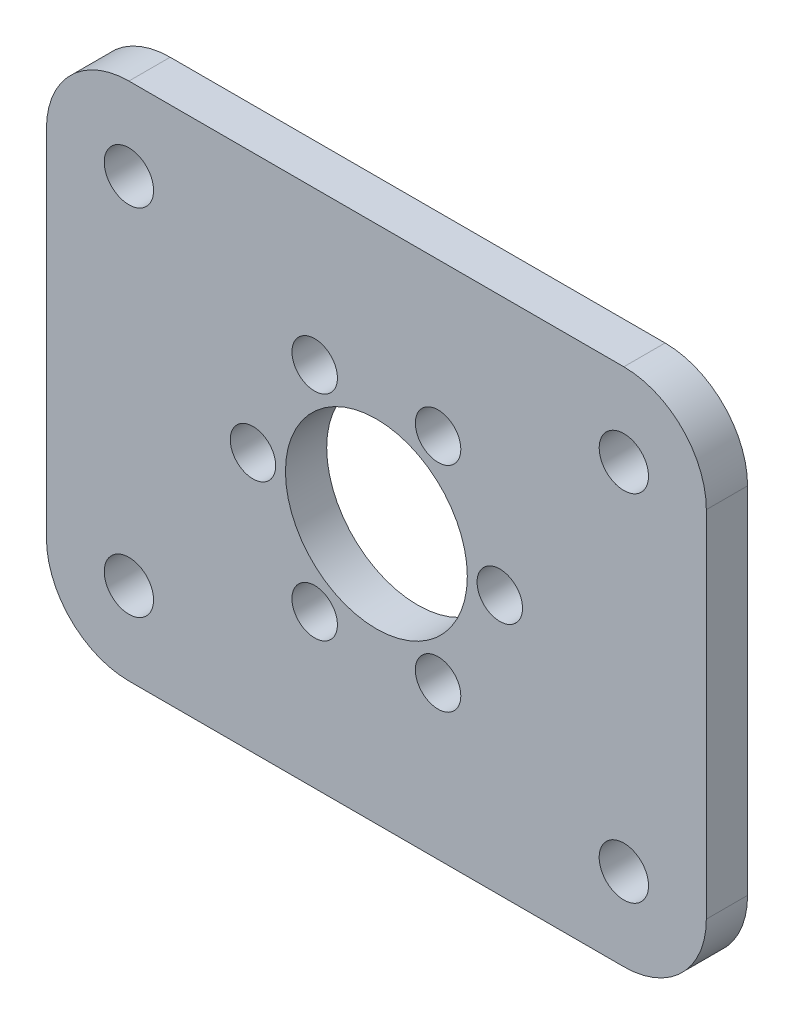
SolidWorks part; units mm, degrees
material "Balsa"
ref_plane "Front" through (0, 0, 0) normal (0, 0, 1) x (1, 0, 0)
ref_plane "Top" through (0, 0, 0) normal (0, 1, 0) x (1, 0, 0)
ref_plane "Right" through (0, 0, 0) normal (1, 0, 0) x (0, 0, -1)
sketch "Sketch1" plane through (0, 0, 0) normal (0, 0, 1) x (1, 0, 0)
  line L0 (25.4, 20) -> (-25.4, 20)
  line L1 (-25.4, 20) -> (-25.4, -20)
  line L2 (-25.4, -20) -> (25.4, -20)
  line L3 (0, 0) -> (0, 20) construction
  line L4 (25.4, 20) -> (25.4, -20)
  line L5 (0, 0) -> (-25.4, 0) construction
  circle A1 centre (0, 0) radius 7
  point P9 (0, -20)
  dimension "D1" = 14
  dimension "D2" = 40
  dimension "D3" = 25.4
extrude "Boss-Extrude1" add sketch "Sketch1" along normal blind 3.175
fillet "Fillet1" radius 6.35 4 edges at (-25.4, -20, 1.5875) (25.4, -20, 1.5875) (25.4, 20, 1.5875) (-25.4, 20, 1.5875)
sketch "Sketch8" plane through (0, 0, 3.175) normal (0, 0, 1) x (1, 0, 0)
  line L0 (-25.4, 0) -> (25.4, 0) construction
  line L1 (0, 0) -> (0, -22.225) construction
  line L3 (-25.4, 13.65) -> (-25.4, -13.65) construction
  line L6 (25.4, -13.65) -> (25.4, 13.65) construction
  line L7 (0, 0) -> (0, 20) construction
  line L8 (19.05, 20) -> (-19.05, 20) construction
  circle A0 centre (22.225, 0) radius 1.5
  circle A2 centre (-22.225, 0) radius 1.5
  circle A4 centre (0, 22.225) radius 1.5 [skipped]
  circle A5 centre (0, -22.225) radius 1.5 [skipped]
  dimension "D2" = 3
  dimension "D1" = 22.225
  dimension "D3" = 4
extrude "Cut-Extrude1" [suppressed] cut sketch "Sketch8" against normal through all
sketch "Sketch9" plane through (0, 0, 3.175) normal (0, 0, 1) x (1, 0, 0)
  line L0 (0, 0) -> (0, 20) construction
  line L1 (19.05, 20) -> (-19.05, 20) construction
  line L2 (0, 0) -> (-25.4, 0) construction
  line L3 (-25.4, 13.65) -> (-25.4, -13.65) construction
  line L4 (0, 0) -> (9.5, 0) construction
  line L5 (4.75, 8.2272) -> (0, 0) construction
  line L6 (0, 0) -> (-4.75, 8.2272) construction
  circle A0 centre (-19.05, 13.65) radius 1.632 construction
  circle A1 centre (-19.05, -13.65) radius 1.632 construction
  circle A2 centre (19.05, -13.65) radius 1.632 construction
  circle A3 centre (19.05, 13.65) radius 1.632 construction
  circle A4 centre (9.5, 0) radius 1.75
  circle A5 centre (4.75, -8.2272) radius 1.75
  circle A6 centre (-4.75, -8.2272) radius 1.75
  circle A7 centre (-9.5, 0) radius 1.75
  circle A8 centre (-4.75, 8.2272) radius 1.75
  circle A9 centre (4.75, 8.2272) radius 1.75
  dimension "D3" = 3.2639
  dimension "D4" = 9.5
  dimension "D6" = 3.5
  dimension "D1" = 6.35
  dimension "D2" = 6.35
  dimension "D5" = 6
extrude "M3-through" cut sketch "Sketch9" against normal through all
other "Move Face2" [suppressed] parameters "D1"=0.1
sketch "Sketch10" plane through (0, 0, 3.175) normal (0, 0, 1) x (1, 0, 0)
  line L0 (-19.05, -20) -> (19.05, -20) construction
  line L1 (25.4, -13.65) -> (25.4, 13.65) construction
  line L2 (0, 0) -> (27.673, 0) construction
  line L3 (0, 0) -> (0, 21.5313) construction
  circle A0 centre (19.05, -13.65) radius 1.8986
  circle A1 centre (19.05, 13.65) radius 1.8986
  circle A2 centre (-19.05, -13.65) radius 1.8986
  circle A3 centre (-19.05, 13.65) radius 1.8986
  dimension "D3" = 3.7973
  dimension "D1" = 6.35
  dimension "D2" = 6.35
extrude "Cut-Extrude2" cut sketch "Sketch10" against normal through all
